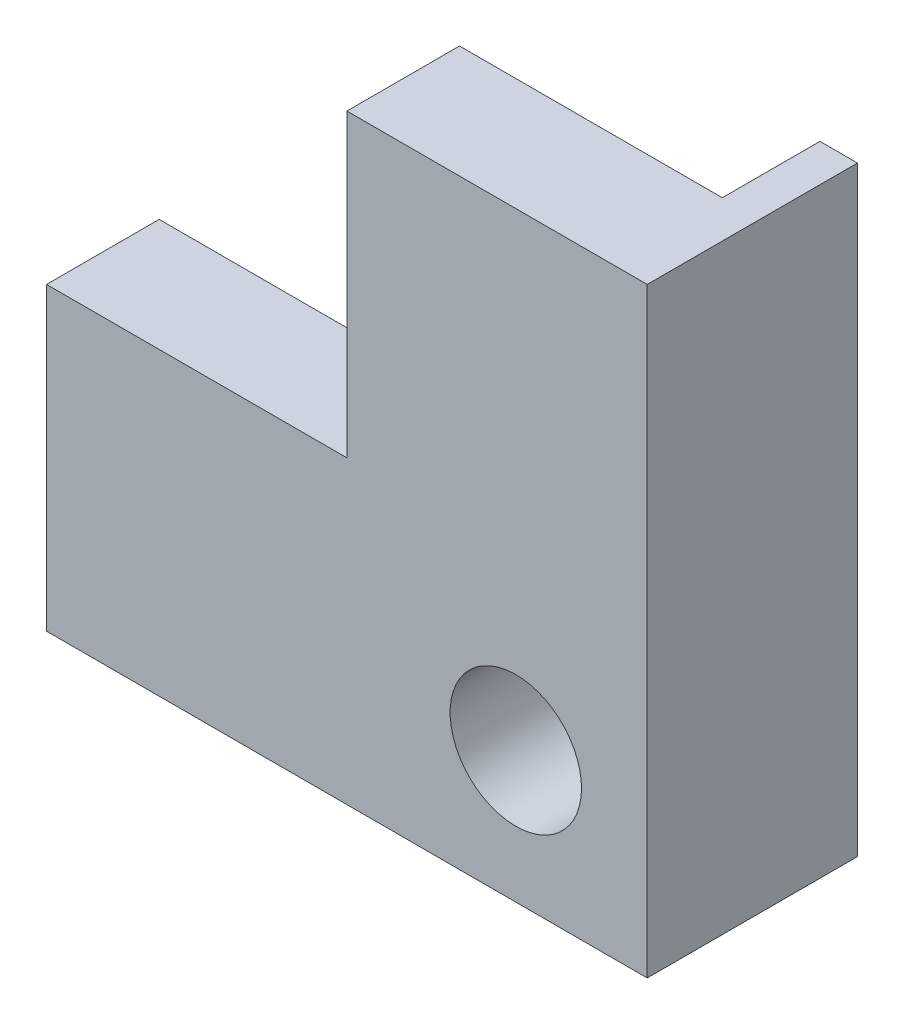
SolidWorks part; units mm, degrees
ref_plane "Plan de face" through (0, 0, 0) normal (0, 0, 1) x (1, 0, 0)
ref_plane "Plan de dessus" through (0, 0, 0) normal (0, 1, 0) x (1, 0, 0)
ref_plane "Plan de droite" through (0, 0, 0) normal (1, 0, 0) x (0, 0, -1)
sketch "Esquisse1" plane through (0, 0, 0) normal (0, 0, 1) x (1, 0, 0)
  line L0 (104.8649, -135.3671) -> (89.8649, -135.3671)
  line L2 (89.8649, -135.3671) -> (89.8649, -128.3671)
  line L4 (89.8649, -128.3671) -> (97.8649, -128.3671)
  line L5 (97.8649, -128.3671) -> (97.8649, -120.3671)
  line L7 (97.8649, -120.3671) -> (104.8649, -120.3671)
  line L9 (104.8649, -120.3671) -> (104.8649, -135.3671)
  circle A0 centre (102.3649, -132.8671) radius 1.75
  dimension "D5" = 3.5
  dimension "D1" = 7
  dimension "D2" = 7
  dimension "D3" = 15
  dimension "D4" = 15
extrude "Boss.-Extru.1" add sketch "Esquisse1" along normal blind 3
sketch "Esquisse2" plane through (0, 0, 3) normal (0, 0, 1) x (1, 0, 0)
  line L0 (89.8649, -135.3671) -> (89.8649, -136.3671)
  line L1 (89.8649, -136.3671) -> (105.8649, -136.3671)
  line L2 (105.8649, -136.3671) -> (105.8649, -120.3671)
  line L3 (105.8649, -120.3671) -> (104.8649, -120.3671)
  line L4 (104.8649, -120.3671) -> (104.8649, -135.3671)
  line L5 (89.8649, -135.3671) -> (104.8649, -135.3671) construction
  line L6 (104.8649, -135.3671) -> (104.8649, -120.3671) construction
  line L7 (104.8649, -135.3671) -> (89.8649, -135.3671)
  dimension "D1" = 1
  dimension "D2" = 1
extrude "Boss.-Extru.2" add sketch "Esquisse2" against normal blind 5.6
sketch "Esquisse3" plane through (0, 0, -2.6) normal (0, 0, -1) x (-1, 0, 0)
  line L0 (-104.8649, -135.3671) -> (-89.8649, -135.3671) construction
  line L1 (-104.8649, -120.3671) -> (-104.8649, -135.3671) construction
  line L2 (-89.8649, -135.3671) -> (-97.3649, -135.3671)
  line L3 (-104.8649, -127.8671) -> (-104.8649, -120.3671)
  arc A0 (-89.8649, -135.3671) -> (-97.3649, -135.3671) centre (-93.6149, -140.7936) ccw
  arc A1 (-104.8649, -120.3671) -> (-104.8649, -127.8671) centre (-110.2914, -124.1171) cw
extrude "Boss.-Extru.3" add sketch "Esquisse3" against normal blind 1
